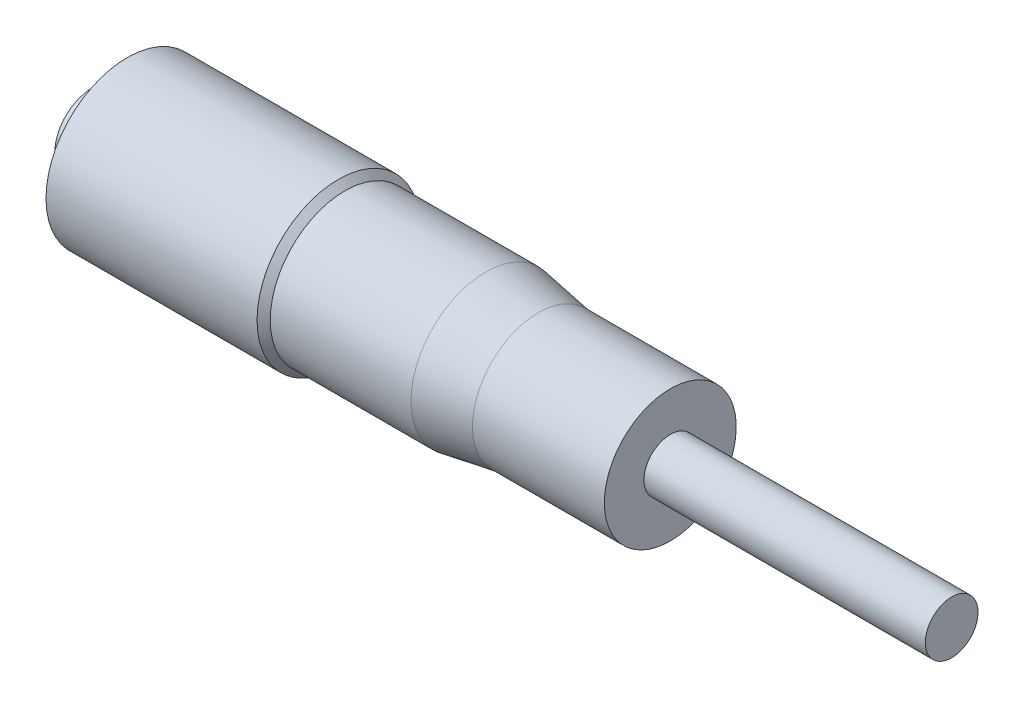
SolidWorks part; units mm, degrees
ref_plane "Front Plane" through (0, 0, 0) normal (0, 0, 1) x (1, 0, 0)
ref_plane "Top Plane" through (0, 0, 0) normal (0, 1, 0) x (1, 0, 0)
ref_plane "Right Plane" through (0, 0, 0) normal (1, 0, 0) x (0, 0, -1)
sketch "Sketch1" plane through (0, 0, 0) normal (0, 0, 1) x (1, 0, 0)
  line L0 (0, 0) -> (88.5234, 0) construction
  line L1 (-49.375, 0) -> (49.375, 0)
  line L2 (49.375, 0) -> (49.375, 3)
  line L3 (49.375, 3) -> (17.375, 3)
  line L4 (17.375, 3) -> (17.375, 7.5)
  line L5 (17.375, 7.5) -> (2.375, 7.5)
  line L6 (2.375, 7.5) -> (-3.625, 8.5)
  line L7 (-3.625, 8.5) -> (-19.625, 8.5)
  line L8 (-19.625, 8.5) -> (-20.375, 9.25)
  line L9 (-20.375, 9.25) -> (-44.375, 9.25)
  line L10 (-44.375, 9.25) -> (-45.875, 4.25)
  line L11 (-45.875, 4.25) -> (-48.375, 4.25)
  arc A0 (-48.375, 4.25) -> (-49.375, 0) centre (-39.8437, 0) ccw
  point P18 (0, 0)
  dimension "D1" = 32
  dimension "D2" = 3
  dimension "D3" = 7.5
  dimension "D4" = 15
  dimension "D5" = 8.5
  dimension "D6" = 6
  dimension "D7" = 9.25
  dimension "D8" = 135
  dimension "D9" = 16
  dimension "D10" = 24
  dimension "D11" = 1.5
  dimension "D12" = 5
  dimension "D13" = 2.5
  dimension "D14" = 1
revolve "Revolve1" add sketch "Sketch1" angle 360 about L0
